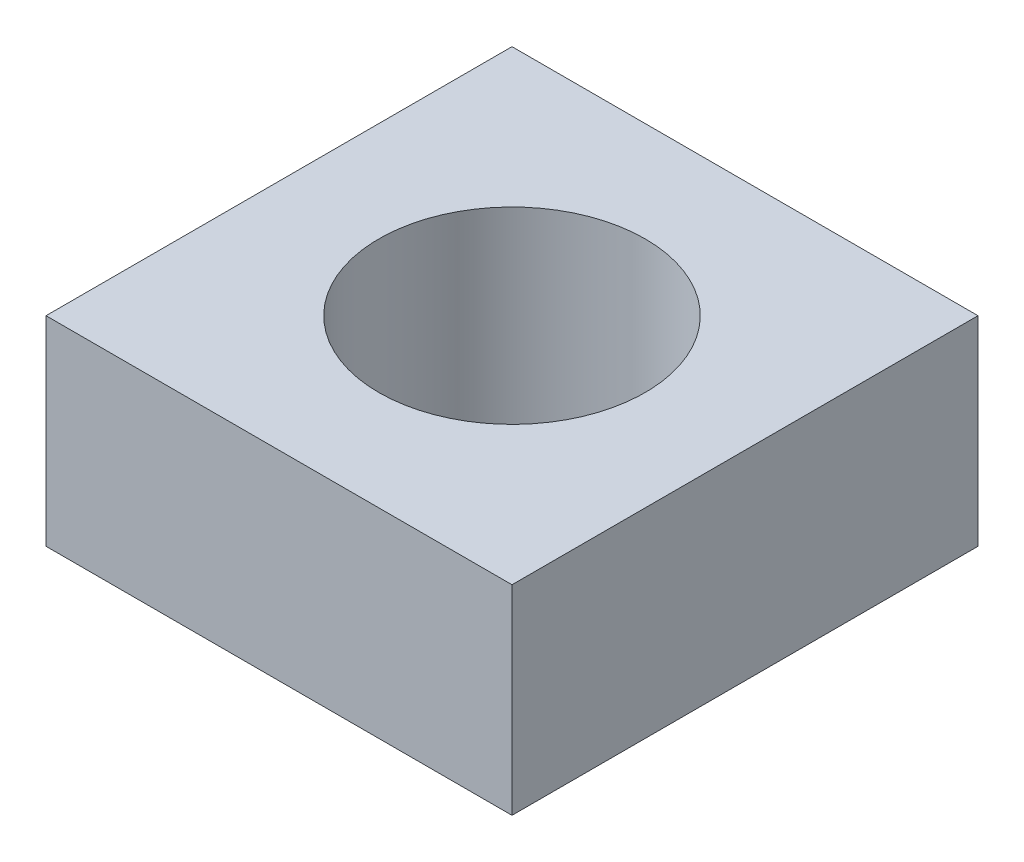
SolidWorks part; units mm, degrees
ref_plane "Front Plane" through (0, 0, 0) normal (0, 0, 1) x (1, 0, 0)
ref_plane "Top Plane" through (0, 0, 0) normal (0, 1, 0) x (1, 0, 0)
ref_plane "Right Plane" through (0, 0, 0) normal (1, 0, 0) x (0, 0, -1)
sketch "Sketch1" plane through (0, 0, 0) normal (0, 0, 1) x (1, 0, 0)
  line L1 (0, 0) -> (22.225, 0)
  line L2 (0, 0) -> (0, 9.525)
  line L3 (0, 9.525) -> (22.225, 9.525)
  line L4 (22.225, 0) -> (22.225, 9.525)
extrude "Boss-Extrude1" add sketch "Sketch1" along normal blind 22.225
sketch "Sketch2" plane through (0, 9.525, 0) normal (0, 1, 0) x (1, 0, 0)
  circle A0 centre (11.1125, -11.1125) radius 6.35
extrude "Cut-Extrude1" cut sketch "Sketch2" against normal blind 22.225
